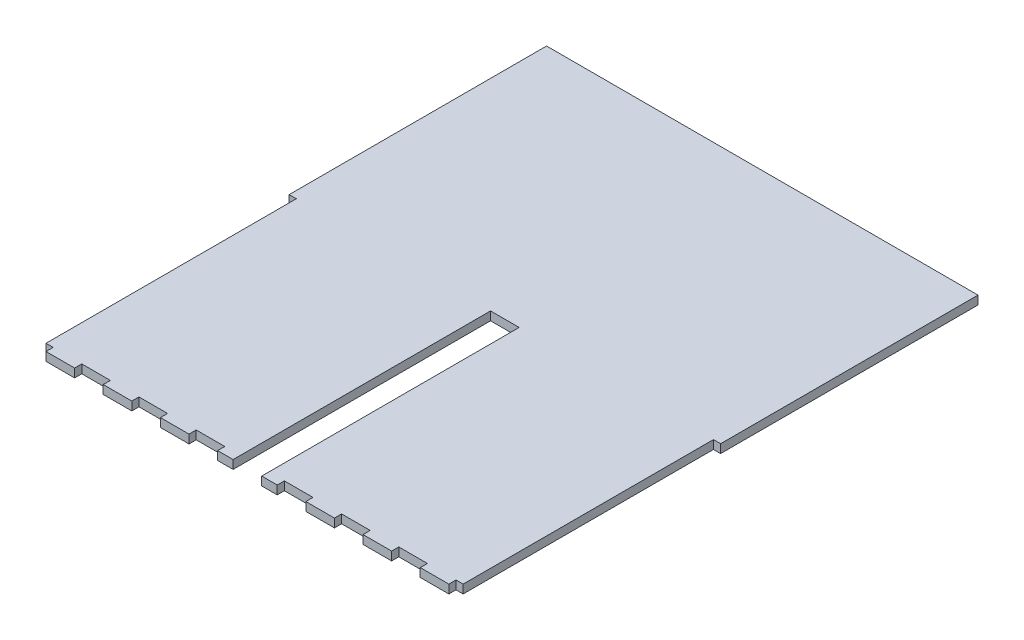
SolidWorks part; units mm, degrees
ref_plane "Front Plane" through (0, 0, 0) normal (0, 0, 1) x (1, 0, 0)
ref_plane "Top Plane" through (0, 0, 0) normal (0, 1, 0) x (1, 0, 0)
ref_plane "Right Plane" through (0, 0, 0) normal (1, 0, 0) x (0, 0, -1)
sketch "Sketch1" plane through (0, 0, 0) normal (0, 1, 0) x (1, 0, 0)
  line L0 (-90.5, 0) -> (-87.5, 0)
  line L2 (-90.5, 0) -> (-90.5, 108)
  line L3 (-90.5, 108) -> (90.5, 108)
  line L4 (90.5, 0) -> (90.5, 108)
  line L5 (-87.5, 0) -> (-87.5, -105)
  line L10 (-84.5, -108) -> (-72.5, -108)
  line L12 (0, 0) -> (0, 108) construction
  line L13 (-87.5, -105) -> (-84.5, -105)
  line L14 (-84.5, -105) -> (-84.5, -108)
  line L15 (-72.5, -108) -> (-72.5, -105)
  line L16 (-72.5, -105) -> (-60.5, -105)
  line L17 (-60.5, -105) -> (-60.5, -108)
  line L18 (-84.5, -105) -> (-72.5, -105) construction
  line L19 (-60.5, -108) -> (-48.5, -108)
  line L20 (-48.5, -108) -> (-48.5, -105)
  line L21 (-48.5, -105) -> (-36.5, -105)
  line L22 (-36.5, -105) -> (-36.5, -108)
  line L23 (-24.5, -108) -> (-24.5, -105)
  line L24 (-24.5, -105) -> (-12.5, -105)
  line L25 (-36.5, -108) -> (-24.5, -108)
  line L26 (-72.5, -108) -> (-48.5, -108) construction
  line L28 (72.5, -108) -> (48.5, -108) construction
  line L29 (84.5, -105) -> (72.5, -105) construction
  line L30 (36.5, -108) -> (24.5, -108)
  line L31 (24.5, -105) -> (12.5, -105)
  line L32 (24.5, -108) -> (24.5, -105)
  line L33 (36.5, -105) -> (36.5, -108)
  line L34 (48.5, -105) -> (36.5, -105)
  line L35 (48.5, -108) -> (48.5, -105)
  line L36 (60.5, -108) -> (48.5, -108)
  line L37 (60.5, -105) -> (60.5, -108)
  line L38 (72.5, -105) -> (60.5, -105)
  line L39 (72.5, -108) -> (72.5, -105)
  line L40 (84.5, -105) -> (84.5, -108)
  line L41 (87.5, -105) -> (84.5, -105)
  line L42 (90.5, 0) -> (87.5, 0)
  line L43 (87.5, 0) -> (87.5, -105)
  line L44 (84.5, -108) -> (72.5, -108)
  line L47 (-6, 0) -> (6, 0)
  line L49 (-12.5, -105) -> (-12.5, -108)
  line L50 (-12.5, -108) -> (-6, -108)
  line L51 (-6, -108) -> (-6, 0)
  line L52 (6, 0) -> (6, -108)
  line L53 (6, -108) -> (12.5, -108)
  line L54 (12.5, -108) -> (12.5, -105)
  line L58 (-12.5, -105) -> (-12.5, -108) [skipped]
  line L59 (-90.5, 0) -> (-90.5, -108) construction
  point P9 (0, 0)
  dimension "D1" = 3
  dimension "D2" = 3
  dimension "D3" = 216
  dimension "D4" = 3
  dimension "D5" = 3
  dimension "D6" = 12
  dimension "D7" = 181
  dimension "D8" = 12
  dimension "D9" = 24
  dimension "D10" = 3
  dimension "D11" = 6.5
extrude "Boss-Extrude1" add sketch "Sketch1" along normal blind 3.6 contours L24 L49 L50 L51 L47 L52 L53 L54 L31 L32 L30 L33 L34 L35 L36 L37 L38 L39 L44 L40 L41 L43 L42 L4 L3 L2 L0 L5 L13 L14 L10 L15 L16 L17 L19 L20 L21 L22 L25 L23
